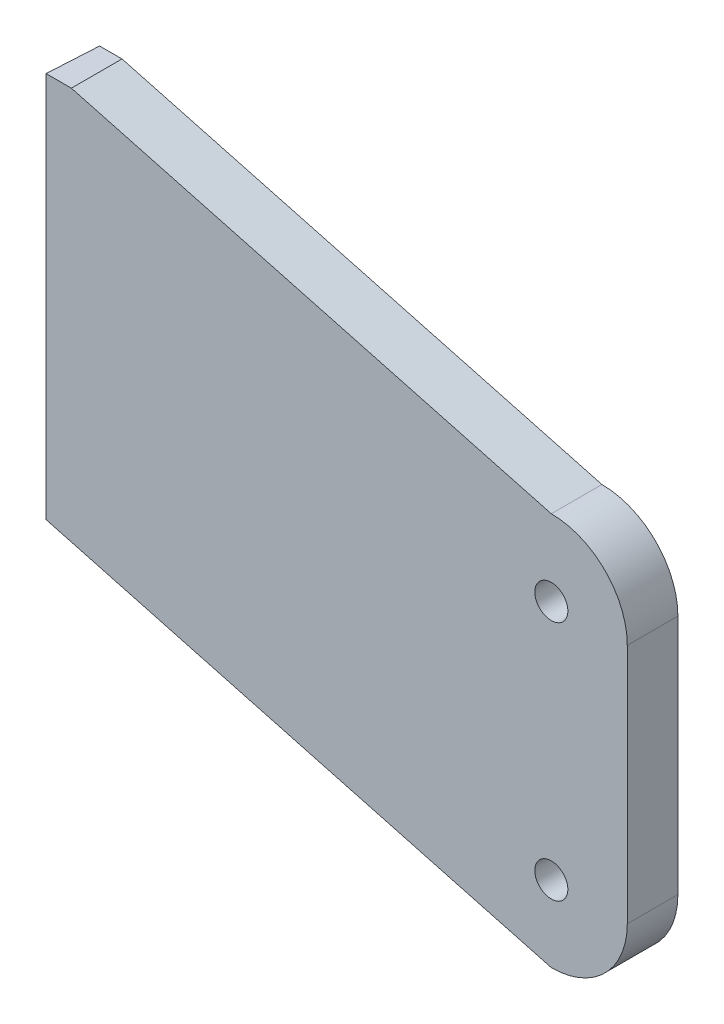
SolidWorks part; units mm, degrees
ref_plane "Front Plane" through (0, 0, 0) normal (0, 0, 1) x (1, 0, 0)
ref_plane "Top Plane" through (0, 0, 0) normal (0, 1, 0) x (1, 0, 0)
ref_plane "Right Plane" through (0, 0, 0) normal (1, 0, 0) x (0, 0, -1)
sketch "Sketch1" plane through (0, 0, 0) normal (0, 0, 1) x (1, 0, 0)
  line L0 (0, -23.8125) -> (0, 23.8125)
  line L1 (-15, -38.8125) -> (-120, -38.8125)
  line L2 (-15, -38.8125) -> (-119.7785, -10.7372)
  line L3 (-15, 38.8125) -> (-119.7785, 66.8878)
  line L4 (-119.7785, -10.7372) -> (-119.7785, 66.8878)
  arc A0 (0, 23.8125) -> (-15, 38.8125) centre (-15, 23.8125) ccw
  circle A1 centre (-15, 23.8125) radius 3.2639
  circle A2 centre (-15, -23.8125) radius 3.2639
  arc A3 (0, -23.8125) -> (-15, -38.8125) centre (-15, -23.8125) cw
  dimension "D2" = 30
  dimension "D3" = 6.5278
  dimension "D7" = 6.5278
  dimension "D1" = 47.625
  dimension "D4" = 105
  dimension "D5" = 15
  dimension "D6" = 108.4747
extrude "Boss-Extrude1" add sketch "Sketch1" along normal blind 10 contours A3 L0 A0 L3 L4 L2 A1 A2
sketch "Sketch2" plane through (0, 0, 10) normal (0, 0, 1) x (1, 0, 0)
  line L0 (-109.7785, 64.2083) -> (-109.7785, 103.7647)
  line L1 (-15, 38.8125) -> (-119.7785, 66.8878) construction
  line L2 (-109.7785, 103.7647) -> (-165.743, 103.7647)
  line L3 (-165.743, 103.7647) -> (-165.743, 64.2083)
  line L4 (-165.743, 64.2083) -> (-109.7785, 64.2083)
  dimension "D1" = 10
extrude "Boss-Extrude2" add sketch "Sketch2" against normal blind 50
ref_plane "Plane1" through (-0.9592, 0, 16.7887) normal (-0.057, 0, 0.9984) x (0, 1, 0)
sketch "Sketch4" plane through (-0.9592, 0, 16.7887) normal (-0.057, 0, 0.9984) x (0, 1, 0)
  line L1 (64.2083, 144.013) -> (64.2083, 119.013)
  line L3 (64.2083, 149.013) -> (64.2083, 176.7001)
  line L4 (64.2083, 164.9027) -> (64.2083, 119.013) construction
  line L5 (64.2083, 176.7001) -> (111.9846, 176.7001)
  line L6 (111.9846, 176.7001) -> (111.9846, 106.9013)
  line L7 (111.9846, 106.9013) -> (64.2083, 106.9013)
  line L8 (64.2083, 106.9013) -> (64.2083, 114.013)
  arc A0 (64.2083, 119.013) -> (64.2083, 144.013) centre (64.2083, 131.513) ccw
  arc A1 (64.2083, 114.013) -> (64.2083, 149.013) centre (64.2083, 131.513) ccw
  dimension "D1" = 25
  dimension "D3" = 35
extrude "Cut-Extrude1" cut sketch "Sketch4" against normal through all and the other way through all contours A1 L8 L7 L6 L5 L3 | L1 A0
fillet "Fillet1" [suppressed] radius 10
sketch "Sketch7" plane through (0, 64.2083, 0) normal (0, 1, 0) x (1, 0, 0)
  line L0 (-119.7785, 0) -> (-119.2071, 0)
  line L1 (-119.2071, 0) -> (-119.7785, -10)
  line L2 (-119.7785, -10) -> (-119.7785, 0)
extrude "Cut-Extrude3" cut sketch "Sketch7" against normal through all
sketch "Sketch8" plane through (0, 64.2083, 0) normal (0, -1, 0) x (1, 0, 0)
  line L0 (-119.2071, 0) -> (-116.9218, -40)
  line L1 (-116.9218, -40) -> (-111.9136, -40)
  line L2 (-111.9136, -40) -> (-114.199, 0)
  line L3 (-114.199, 0) -> (-119.2071, 0)
extrude "Boss-Extrude3" add sketch "Sketch8" along normal up to surface (77.0529 mm away)
sketch "Sketch10" plane through (-113.8274, 0, -6.5035) normal (0.9984, 0, 0.057) x (0.057, 0, -0.9984)
  circle A0 centre (83.4725, -10.6773) radius 90
extrude "Cut-Extrude4" cut sketch "Sketch10" against normal blind 50
fillet "Fillet4" [suppressed] radius 5
sketch "Sketch14" plane through (-0.9592, 0, 16.7887) normal (-0.057, 0, 0.9984) x (0, 1, 0)
  line L0 (64.2083, 114.013) -> (103.7071, 114.013)
  line L1 (103.7071, 114.013) -> (103.7071, 158.8205)
  line L2 (103.7071, 158.8205) -> (-53.0931, 158.8205)
  line L3 (-53.0931, 158.8205) -> (-49.031, 114.013)
  line L4 (-49.031, 114.013) -> (64.2083, 114.013)
extrude "Cut-Extrude6" cut sketch "Sketch14" against normal through all and the other way through all
